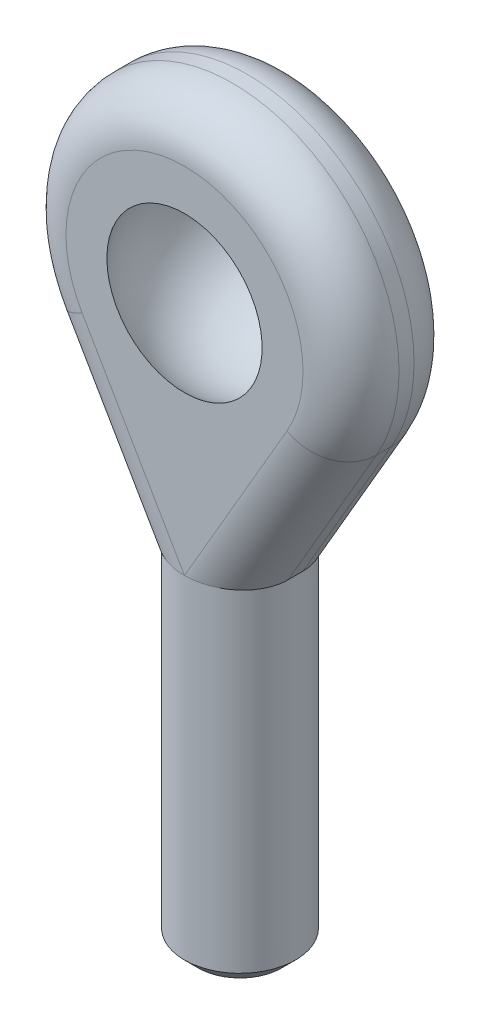
SolidWorks part; units mm, degrees
material "Alloy Steel"
ref_plane "Front Plane" through (0, 0, 0) normal (0, 0, 1) x (1, 0, 0)
ref_plane "Top Plane" through (0, 0, 0) normal (0, 1, 0) x (1, 0, 0)
ref_plane "Right Plane" through (0, 0, 0) normal (1, 0, 0) x (0, 0, -1)
sketch "Sketch1" plane through (0, 0, 0) normal (0, 1, 0) x (1, 0, 0)
  circle A0 centre (0, 0) radius 4
  dimension "D1" = 8
extrude "Boss-Extrude1" add sketch "Sketch1" along normal mid plane 25
sketch "Sketch10" plane through (0, 0, 0) normal (0, 0, 1) x (1, 0, 0)
  line L0 (0, 0) -> (0, -50000) construction
  line L2 (-4, -12.5) -> (4, -12.5) construction
  line L5 (-10.3753, 23.4707) -> (-4, 12.5)
  line L6 (4, 12.5) -> (10.3753, 23.4707)
  line L12 (4, 12.5) -> (-4, 12.5)
  line L13 (4, 12.5) -> (-4, 12.5) construction
  line L14 (-4, 12.5) -> (-4, -12.5) construction
  circle A4 centre (0, 29.5) radius 12 construction
  arc A5 (-10.3753, 23.4707) -> (10.3753, 23.4707) centre (0, 29.5) cw
  point P6 (0, 0)
  dimension "D2" = 24
  dimension "D1" = 42
extrude "Boss-Extrude6" add sketch "Sketch10" along normal mid plane 8
chamfer "Chamfer1" distance 1 angle 45 1 edges at (0, -12.5, 4)
sketch "Sketch11" plane through (0, 0, 0) normal (1, 0, 0) x (0, 0, -1)
  line L0 (-4, 29.5) -> (4, 29.5) construction
  line L1 (-4.5, 29.5) -> (4.5, 29.5)
  line L4 (-4, 41.5) -> (-4, 23.4707) construction
  line L5 (4, 23.4707) -> (4, 41.5) construction
  line L6 (-3, -12.5) -> (3, -12.5) construction
  line L7 (0, 0) -> (0, -50000) construction
  line L8 (-4.5, 29.5) -> (-4.5, 34.7)
  line L9 (4.5, 34.7) -> (4.5, 29.5)
  arc A0 (-4.5, 34.7) -> (4.5, 34.7) centre (0, 29.5) cw
  circle A1 centre (0, 29.5) radius 6.8768 construction
  dimension "D1" = 42
  dimension "D2" = 10.4
  dimension "D4" = 9
sketch "Sketch12" plane through (0, 0, 0) normal (1, 0, 0) x (0, 0, -1)
  line L0 (-4, 29.5) -> (4, 29.5) construction
  line L1 (-3, -12.5) -> (3, -12.5) construction
  line L2 (4, 23.4707) -> (4, 41.5) construction
  line L7 (0, 0) -> (0, -50000) construction
  line L8 (-4.5, 33.5) -> (-4.5, 34.7)
  line L9 (4.5, 34.7) -> (4.5, 33.5)
  line L10 (4.5, 33.5) -> (-4.5, 33.5)
  arc A0 (-4.5, 34.7) -> (4.5, 34.7) centre (0, 29.5) cw
  circle A1 centre (0, 29.5) radius 6.8768 construction
  point P15 (0, 33.5)
  dimension "D1" = 42
  dimension "D2" = 10.4
  dimension "D3" = 8
  dimension "D4" = 9
revolve "Cut-Revolve1" cut sketch "Sketch11" angle 360 about L1
fillet "Fillet6" radius 3.4584 6 edges at (-7.1877, 17.9853, 4) (0, 41.5, 4) (7.1877, 17.9853, 4) (7.1877, 17.9853, -4) (0, 41.5, -4) (-7.1877, 17.9853, -4)
